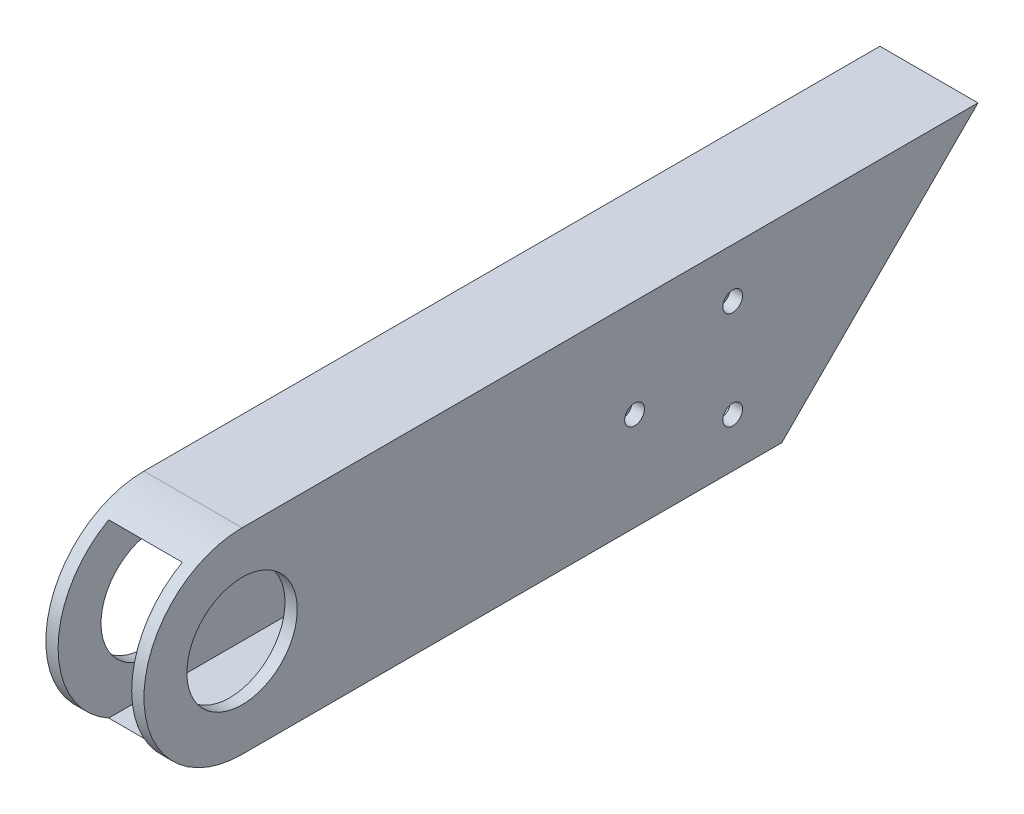
SolidWorks part; units mm, degrees
ref_plane "Front Plane" through (0, 0, 0) normal (0, 0, 1) x (1, 0, 0)
ref_plane "Top Plane" through (0, 0, 0) normal (0, 1, 0) x (1, 0, 0)
ref_plane "Right Plane" through (0, 0, 0) normal (1, 0, 0) x (0, 0, -1)
sketch "Sketch1" plane through (0, 0, 0) normal (0, 0, 1) x (1, 0, 0)
  line L2 (-22.225, 47.625) -> (-3.175, 47.625)
  line L3 (-22.225, 47.625) -> (-22.225, 3.175)
  line L4 (-22.225, 3.175) -> (-3.175, 3.175)
  line L5 (-3.175, 47.625) -> (-3.175, 3.175)
  line L6 (-25.4, 50.8) -> (0, 50.8)
  line L7 (-25.4, 50.8) -> (-25.4, 0)
  line L8 (-25.4, 0) -> (0, 0)
  line L9 (0, 50.8) -> (0, 0)
  dimension "D1" = 25.4
  dimension "D2" = 50.8
  dimension "D3" = 3.175
  dimension "D4" = 3.175
  dimension "D5" = 3.175
  dimension "D6" = 3.175
extrude "Boss-Extrude1" add sketch "Sketch1" along normal blind 215.9
sketch "Sketch2" plane through (0, 0, 0) normal (1, 0, 0) x (0, 0, -1)
  line L0 (0, 50.8) -> (-50.8, 0)
  line L1 (-215.9, 0) -> (0, 0) construction
  line L2 (-50.8, 0) -> (0, 0)
  line L3 (0, 0) -> (0, 50.8)
  line L4 (-215.9, 0) -> (-215.9, 50.8) construction
  dimension "D1" = 165.1
extrude "Cut-Extrude1" cut sketch "Sketch2" against normal blind 25.4
sketch "Sketch3" plane through (0, 0, 0) normal (1, 0, 0) x (0, 0, -1)
  line L0 (-50.8, 0) -> (-50.8, 50.8) construction
  line L1 (-215.9, 50.8) -> (0, 50.8) construction
  line L2 (-88.9, 25.4) -> (-63.5, 25.4) construction
  line L3 (-63.5, 38.1) -> (-63.5, 12.7) construction
  circle A0 centre (-63.5, 38.1) radius 2.5527
  circle A1 centre (-63.5, 12.7) radius 2.5527
  circle A2 centre (-88.9, 25.4) radius 2.5527
  point P11 (-50.8, 25.4)
  dimension "D3" = 5.1054
  dimension "D1" = 25.4
  dimension "D2" = 25.4
  dimension "D4" = 12.7
extrude "Cut-Extrude2" cut sketch "Sketch3" against normal blind 25.4
sketch "Sketch6" plane through (0, 0, 0) normal (1, 0, 0) x (0, 0, -1)
  line L0 (-215.9, 50.8) -> (0, 50.8) construction
  line L1 (-215.9, 0) -> (-50.8, 0) construction
  line L3 (-215.9, 0) -> (-215.9, 50.8) construction
  arc A0 (-190.5, 0) -> (-190.5, 50.8) centre (-190.5, 25.4) cw
extrude "Cut-Extrude-Thin1" cut sketch "Sketch6" against normal through all flip side to cut thin thin type one direction reverse wall 12.7
sketch "Sketch7" plane through (0, 0, 0) normal (1, 0, 0) x (0, 0, -1)
  line L0 (-190.5, 50.8) -> (-190.5, 0) construction
  circle A0 centre (-190.5, 25.4) radius 14.2875
  dimension "D1" = 28.575
extrude "Cut-Extrude3" cut sketch "Sketch7" against normal blind 25.4
